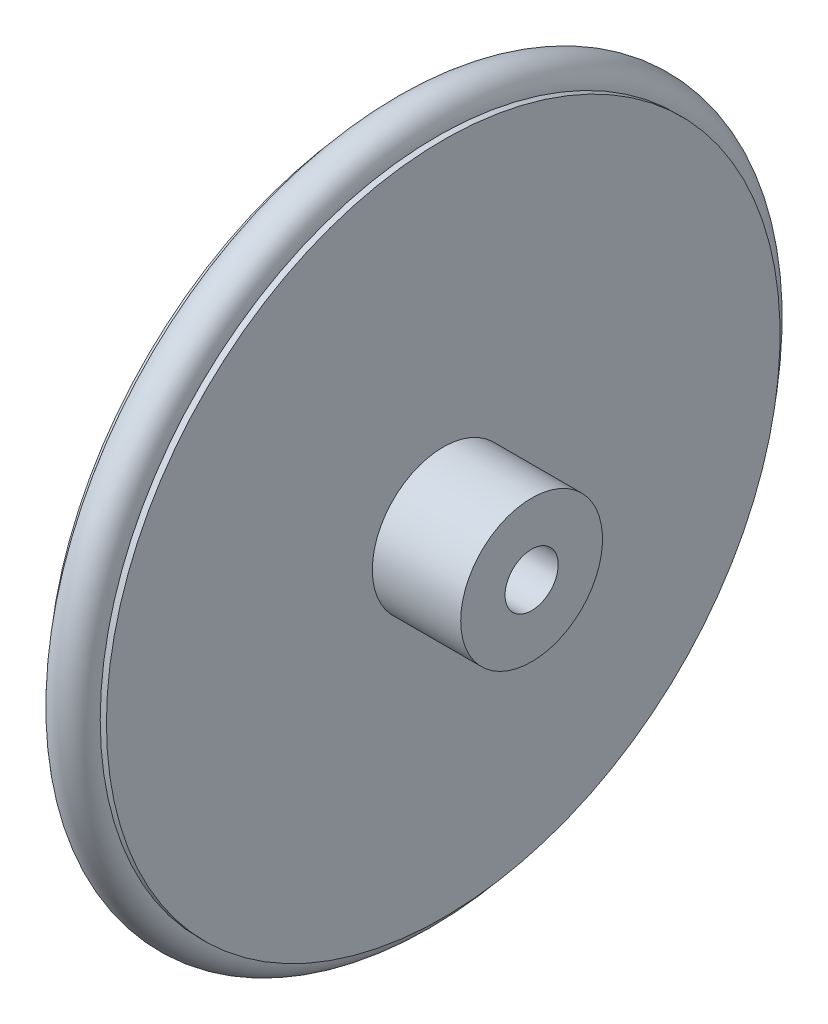
SolidWorks part; units mm, degrees
ref_plane "Plan de face" through (0, 0, 0) normal (0, 0, 1) x (1, 0, 0)
ref_plane "Plan de dessus" through (0, 0, 0) normal (0, 1, 0) x (1, 0, 0)
ref_plane "Plan de droite" through (0, 0, 0) normal (1, 0, 0) x (0, 0, -1)
sketch "Esquisse1" plane through (0, 0, 0) normal (0, 0, 1) x (1, 0, 0)
  line L0 (0, 0) -> (16.57, 0)
  line L1 (16.57, 0) -> (16.57, 8)
  line L2 (16.57, 8) -> (6.6, 8)
  line L3 (6.6, 8) -> (6.6, 38)
  line L4 (6.6, 38) -> (5.9, 38)
  line L5 (5.9, 38) -> (5.9, 35)
  line L6 (5.9, 35) -> (0.7, 35)
  line L7 (0.7, 35) -> (0.7, 38)
  line L8 (0.7, 38) -> (0, 38)
  line L9 (0, 38) -> (0, 0)
  line L10 (-19.9451, 0) -> (43.8468, 0) construction
  dimension "D1" = 16.57
  dimension "D2" = 0.7
  dimension "D3" = 0.7
  dimension "D4" = 6.6
  dimension "D5" = 3
  dimension "D6" = 8
  dimension "D7" = 38
  dimension "D8" = 38
revolve "Révolution1" add sketch "Esquisse1" angle 360 about L10
sketch "Esquisse2" plane through (16.57, 0, 0) normal (1, 0, 0) x (0, 0, -1)
  circle A0 centre (0, 0) radius 3
  dimension "D1" = 6
extrude "Enlèv. mat.-Extru.1" cut sketch "Esquisse2" against normal through all
ref_plane "Plan1" through (3.3, 0, 0) normal (1, 0, 0) x (0, 0, -1)
sketch "Esquisse4" plane through (3.3, 0, 0) normal (1, 0, 0) x (0, 0, -1)
  circle A0 centre (0, 0) radius 38.5
  dimension "D1" = 77
sketch "Esquisse5" plane through (0, 0, 0) normal (0, 0, 1) x (1, 0, 0)
  line L0 (3.3, -38.5) -> (3.3, 38.5) construction
  line L1 (5.9, 35) -> (0.7, 35) construction
  circle A0 centre (3.3, 38) radius 2.5
  dimension "D1" = 5
  dimension "D2" = 3
sweep "Balayage1" add profiles "Esquisse5" path "Esquisse4"
